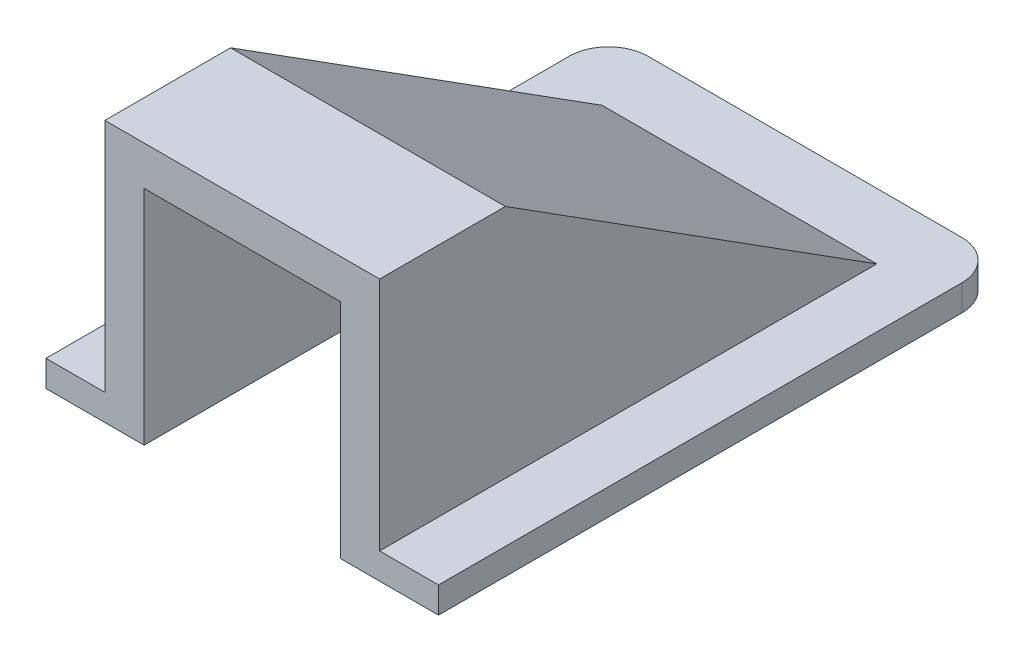
SolidWorks part; units mm, degrees
ref_plane "Alzado" through (0, 0, 0) normal (0, 0, 1) x (1, 0, 0)
ref_plane "Planta" through (0, 0, 0) normal (0, 1, 0) x (1, 0, 0)
ref_plane "Vista lateral" through (0, 0, 0) normal (1, 0, 0) x (0, 0, -1)
sketch "Croquis2" plane through (0, 0, 0) normal (1, 0, 0) x (0, 0, -1)
  line L1 (-41.2833, 1.4772) -> (1.7167, 1.4772)
  line L2 (-41.2833, 1.4772) -> (-41.2833, -28.5228)
  line L3 (-41.2833, -28.5228) -> (1.7167, -28.5228)
  line L4 (1.7167, 1.4772) -> (1.7167, -28.5228)
  dimension "D1" = 30
  dimension "D2" = 43
extrude "Saliente-Extruir1" add sketch "Croquis2" along normal blind 30
sketch "Croquis3" plane through (30, 0, 0) normal (1, 0, 0) x (0, 0, -1)
  line L0 (-41.2833, 1.4772) -> (-41.2833, -28.5228) construction
  line L1 (-38.2833, -44.0813) -> (4.2461, -44.0813)
  line L2 (-38.2833, -44.0813) -> (-38.2833, -18.5228)
  line L3 (-38.2833, -18.5228) -> (4.2461, -18.5228)
  line L4 (4.2461, -44.0813) -> (4.2461, -18.5228)
  line L5 (-41.2833, -28.5228) -> (1.7167, -28.5228) construction
  line L6 (-31.6751, 1.4772) -> (-3.2833, -16.5228)
  line L7 (1.7167, 1.4772) -> (-41.2833, 1.4772) construction
  line L8 (-3.2833, -16.5228) -> (1.7167, -16.5228)
  line L9 (1.7167, -28.5228) -> (1.7167, 1.4772) construction
  line L10 (1.7167, -16.5228) -> (1.7167, 1.4772)
  line L11 (1.7167, 1.4772) -> (-31.6751, 1.4772)
  dimension "D1" = 3
  dimension "D2" = 10
  dimension "D3" = 2
  dimension "D4" = 5
extrude "Cortar-Extruir1" cut sketch "Croquis3" against normal blind 30
sketch "Croquis4" plane through (30, 0, 0) normal (1, 0, 0) x (0, 0, -1)
  line L0 (-41.2833, -1.5228) -> (-32.5459, -1.5228)
  line L1 (-41.2833, 1.4772) -> (-41.2833, -28.5228) construction
  line L2 (-32.5459, -1.5228) -> (-8.8861, -16.5228)
  line L3 (-8.8861, -16.5228) -> (-41.2833, -16.5228)
  line L4 (-41.2833, -16.5228) -> (-41.2833, -1.5228)
  line L5 (-31.6751, 1.4772) -> (-41.2833, 1.4772) construction
  line L6 (1.7167, -18.5228) -> (-38.2833, -18.5228) construction
  line L7 (-31.6751, 1.4772) -> (-3.2833, -16.5228) construction
  dimension "D1" = 3
  dimension "D2" = 2
  dimension "D3" = 3
extrude "Cortar-Extruir2" cut sketch "Croquis4" against normal offset from surface (15 mm away) 7.5 from offset 7.5 up to face at (0, -15.5228, 23.8322) offset against normal yes
sketch "Croquis5" plane through (30, 0, 0) normal (1, 0, 0) x (0, 0, -1)
  line L1 (-3.2833, -16.5228) -> (-41.2833, -16.5228)
  line L8 (-38.2833, -28.5228) -> (-38.2833, -18.5228)
  line L9 (-38.2833, -18.5228) -> (1.7167, -18.5228)
  line L10 (1.7167, -18.5228) -> (1.7167, -16.5228)
  line L11 (1.7167, -16.5228) -> (-3.2833, -16.5228)
  line L12 (-3.2833, -16.5228) -> (-31.6751, 1.4772)
  line L13 (-31.6751, 1.4772) -> (-41.2833, 1.4772)
  line L14 (-41.2833, 1.4772) -> (-41.2833, -28.5228)
  line L15 (-41.2833, -28.5228) -> (-38.2833, -28.5228)
  line L20 (-3.2833, -16.5228) -> (-31.6751, 1.4772)
  line L21 (-31.6751, 1.4772) -> (-41.2833, 1.4772)
  line L22 (-41.2833, 1.4772) -> (-41.2833, -16.5228)
  dimension "D1" = 0
extrude "Cortar-Extruir4" cut sketch "Croquis5" against normal blind 4.5
sketch "Croquis6" plane through (0, 0, 0) normal (-1, 0, 0) x (0, 0, 1)
  line L0 (3.2833, -16.5228) -> (41.2833, -16.5228)
  line L8 (-1.7167, -18.5228) -> (38.2833, -18.5228)
  line L9 (38.2833, -18.5228) -> (38.2833, -28.5228)
  line L10 (38.2833, -28.5228) -> (41.2833, -28.5228)
  line L11 (41.2833, -28.5228) -> (41.2833, 1.4772)
  line L12 (41.2833, 1.4772) -> (31.6751, 1.4772)
  line L13 (31.6751, 1.4772) -> (3.2833, -16.5228)
  line L14 (3.2833, -16.5228) -> (-1.7167, -16.5228)
  line L15 (-1.7167, -16.5228) -> (-1.7167, -18.5228)
  line L19 (41.2833, -16.5228) -> (41.2833, 1.4772)
  line L20 (41.2833, 1.4772) -> (31.6751, 1.4772)
  line L21 (31.6751, 1.4772) -> (3.2833, -16.5228)
  dimension "D1" = 0
extrude "Cortar-Extruir5" cut sketch "Croquis6" against normal blind 4.5
fillet "Redondeo1" radius 3 2 edges at (30, -17.5228, -1.7167) (0, -17.5228, -1.7167)
sketch "Croquis8" plane through (0, -16.5228, 0) normal (0, 1, 0) x (1, 0, 0)
  line L4 (7.5, -8.8861) -> (7.5, -41.2833)
  line L5 (7.5, -41.2833) -> (22.5, -41.2833)
  line L6 (22.5, -41.2833) -> (22.5, -8.8861)
  line L7 (22.5, -8.8861) -> (7.5, -8.8861)
  line L8 (7.5, -8.8861) -> (7.5, -41.2833)
  line L9 (7.5, -41.2833) -> (22.5, -41.2833)
  line L10 (22.5, -41.2833) -> (22.5, -8.8861)
  line L11 (22.5, -8.8861) -> (7.5, -8.8861)
  dimension "D1" = 0
extrude "Cortar-Extruir6" cut sketch "Croquis8" against normal blind 4.5
sketch "Croquis9" plane through (0, -18.5228, 0) normal (0, -1, 0) x (1, 0, 0)
  line L1 (77.7572, 22.6846) -> (-42.526, 22.6846)
  line L2 (77.7572, 22.6846) -> (77.7572, 101.4947)
  line L3 (77.7572, 101.4947) -> (-42.526, 101.4947)
  line L4 (-42.526, 22.6846) -> (-42.526, 101.4947)
extrude "Cortar-Extruir7" cut sketch "Croquis9" along normal blind 22.5
